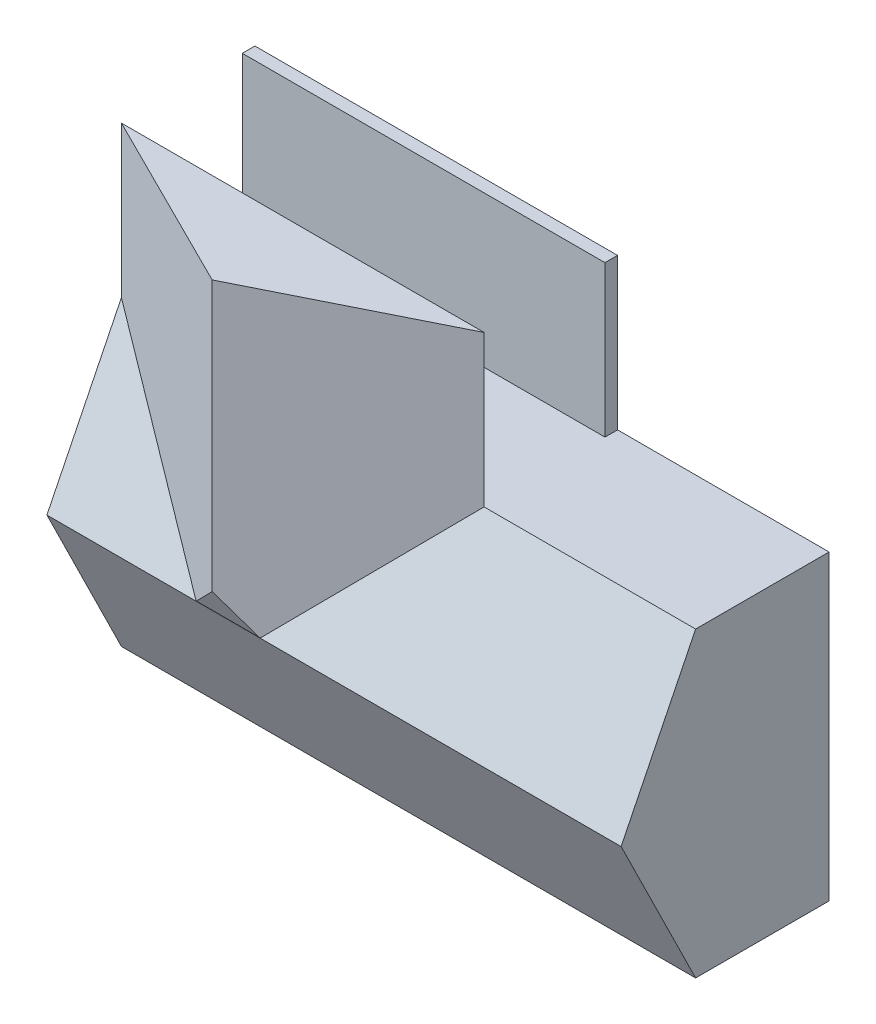
SolidWorks part; units mm, degrees
ref_plane "Front Plane" through (0, 0, 0) normal (0, 0, 1) x (1, 0, 0)
ref_plane "Top Plane" through (0, 0, 0) normal (0, 1, 0) x (1, 0, 0)
ref_plane "Right Plane" through (0, 0, 0) normal (1, 0, 0) x (0, 0, -1)
sketch "Sketch3" plane through (0, 0, 0) normal (0, 0, 1) x (1, 0, 0)
  line L0 (152.4, 152.4) -> (4550.005, 152.4)
  line L1 (0, 0) -> (11582.4, 0)
  line L2 (0, 0) -> (0, 6096)
  line L3 (0, 6096) -> (11582.4, 6096)
  line L4 (11582.4, 0) -> (11582.4, 6096)
  line L5 (4550.005, 152.4) -> (4550.005, 2596.7986)
  line L6 (4550.005, 2596.7986) -> (5842, 2596.7986)
  line L7 (11582.4, 6096) -> (7620, 6096) construction
  line L8 (7620, 6096) -> (5842, 6096) construction
  line L9 (5842, 5943.6) -> (5842, 3511.1986)
  line L10 (5943.6, 3511.1986) -> (10284.7543, 3511.1986)
  line L11 (7620, 5943.6) -> (7620, 3612.7986)
  line L12 (4550.005, 2596.7986) -> (5842, 2596.7986) construction
  line L13 (7315.2, 2495.1986) -> (7315.2, 152.4)
  line L14 (5842, 3511.1986) -> (5842, 2596.7986)
  line L15 (10386.3543, 3511.1986) -> (10386.3543, 2596.7986)
  line L16 (9786.5812, 3511.1986) -> (9786.5812, 2596.7986) construction
  line L17 (0, 6096) -> (0, 9448.8) construction
  line L18 (0, 9448.8) -> (6388.492, 9448.8) construction
  line L19 (6388.492, 9448.8) -> (6388.492, 6096) construction
  line L20 (11430, 152.4) -> (11430, 2495.1986)
  line L21 (3310.1163, 2590.8) -> (0, 2590.8) construction
  line L22 (152.4, 5943.6) -> (5842, 5943.6)
  line L23 (152.4, 152.4) -> (152.4, 5943.6)
  line L24 (4651.605, 152.4) -> (4651.605, 2495.1986)
  line L25 (4651.605, 2495.1986) -> (7315.2, 2495.1986)
  line L26 (7416.8, 2495.1986) -> (7416.8, 152.4)
  line L27 (10284.7543, 3511.1986) -> (10284.7543, 2596.7986)
  line L28 (5943.6, 3612.7986) -> (7620, 3612.7986)
  line L29 (5943.6, 5943.6) -> (5943.6, 3612.7986)
  line L30 (7721.6, 5943.6) -> (7721.6, 3612.7986)
  line L31 (7620, 6096) -> (7620, 3505.2) construction
  line L32 (7721.6, 6096) -> (7721.6, 3505.2) construction
  line L33 (5842, 6096) -> (5842, 3511.1986) construction
  line L34 (5943.6, 6096) -> (5943.6, 3511.1986) construction
  line L35 (5943.6, 5943.6) -> (7620, 5943.6)
  line L36 (152.4, 5943.6) -> (11430, 5943.6) construction
  line L37 (7721.6, 5943.6) -> (11430, 5943.6)
  line L38 (5842, 3612.7986) -> (11582.4, 3612.7986) construction
  line L39 (7721.6, 3612.7986) -> (11430, 3612.7986)
  line L40 (11430, 3612.7986) -> (11430, 5943.6)
  line L41 (11430, 152.4) -> (11430, 5943.6) construction
  line L42 (5842, 3511.1986) -> (11582.4, 3511.1986) construction
  line L43 (10386.3543, 3511.1986) -> (11430, 3511.1986)
  line L44 (10386.3543, 2596.7986) -> (11430, 2596.7986)
  line L45 (4550.005, 2596.7986) -> (11582.4, 2596.7986) construction
  line L46 (11430, 2596.7986) -> (11430, 3511.1986)
  line L47 (4651.605, 2495.1986) -> (11582.4, 2495.1986) construction
  line L48 (7315.2, 2596.7986) -> (7315.2, 0) construction
  line L49 (7416.8, 2596.7986) -> (7416.8, 0) construction
  line L50 (7416.8, 2495.1986) -> (11430, 2495.1986)
  line L51 (7416.8, 152.4) -> (11430, 152.4)
  line L52 (152.4, 152.4) -> (11430, 152.4) construction
  line L53 (4550.005, 0) -> (4550.005, 2596.7986) construction
  line L54 (4651.605, 0) -> (4651.605, 2495.1986) construction
  line L55 (4651.605, 152.4) -> (7315.2, 152.4)
  line L56 (5943.6, 3511.1986) -> (5943.6, 2596.7986)
  line L57 (5943.6, 2596.7986) -> (10284.7543, 2596.7986)
  line L58 (5943.6, 2596.7986) -> (7315.2, 2596.7986) construction
  dimension "D1" = 11582.4
  dimension "D2" = 6096
  dimension "D4" = 3962.4
  dimension "D5" = 1778
  dimension "D7" = 914.4
  dimension "D8" = 152.4
  dimension "D9" = 101.6
  dimension "D10" = 101.6
  dimension "D11" = 101.6
  dimension "D12" = 101.6
  dimension "D13" = 101.6
extrude "Boss-Extrude1" add sketch "Sketch3" along normal blind 2438.4 contours L1 L4 L3 L2 L55 L24 L25 L13 L51 L26 L50 L20 L46 L44 L15 L43 L40 L39 L30 L37 L10 L27 L6 L5 L0 L23 L22 L9 L29 L35 L11 L28
sketch "Sketch4" plane through (0, 0, 0) normal (0, 0, -1) x (-1, 0, 0)
  line L1 (-11582.4, 6096) -> (0, 6096)
  line L2 (-11582.4, 6096) -> (-11582.4, 0)
  line L3 (-11582.4, 0) -> (0, 0)
  line L4 (0, 6096) -> (0, 0)
extrude "Boss-Extrude2" add sketch "Sketch4" along normal blind 254
sketch "Sketch5" plane through (0, 0, 0) normal (0, 0, 1) x (1, 0, 0)
  line L1 (3330.805, 2596.7986) -> (152.4, 2596.7986)
  line L2 (152.4, 152.4) -> (152.4, 5943.6) construction
  line L3 (152.4, 2596.7986) -> (152.4, 2495.1986)
  line L4 (152.4, 152.4) -> (152.4, 5943.6) construction
  line L5 (152.4, 2495.1986) -> (3330.805, 2495.1986)
  line L6 (3330.805, 2495.1986) -> (3330.805, 2596.7986)
extrude "Boss-Extrude3" add sketch "Sketch5" along normal blind 1016
sketch "Sketch6" plane through (0, 0, 0) normal (-1, 0, 0) x (0, 0, 1)
  line L0 (2438.4, 6096) -> (2438.4, 0)
  line L1 (2438.4, 6096) -> (3941.5073, 3048)
  line L2 (2438.4, 3048) -> (3941.5073, 3048) construction
  line L3 (3941.5073, 3048) -> (2438.4, 0)
  dimension "D1" = 26.25
extrude "Boss-Extrude4" add sketch "Sketch6" against normal up to surface (11582.4 mm away) up to face at (11582.4, 3048, 1092.2)
sketch "Sketch7" plane through (0, 6096, 0) normal (0, 1, 0) x (1, 0, 0)
  line L0 (0, 254) -> (7315.2, 254) construction
  line L1 (0, 254) -> (11582.4, 254) construction
  line L2 (7315.2, 254) -> (7315.2, -2438.4) construction
  line L3 (0, -2438.4) -> (11582.4, -2438.4) construction
  line L4 (7937.8596, -2438.4) -> (5791.2, -3941.5073)
  line L5 (11582.4, -3941.5073) -> (0, -3941.5073) construction
  line L6 (5791.2, -3941.5073) -> (5791.2, -2438.4) construction
  line L7 (3644.5404, -2438.4) -> (5791.2, -3941.5073)
  line L8 (7937.8596, -2438.4) -> (3644.5404, -2438.4)
  dimension "D1" = 55
sketch "Sketch8" plane through (0, 0, -254) normal (0, 0, -1) x (-1, 0, 0)
  line L1 (0, 6096) -> (-7315.2, 6096)
  line L2 (0, 6096) -> (0, 9144)
  line L3 (0, 9144) -> (-7315.2, 9144)
  line L4 (-7315.2, 6096) -> (-7315.2, 9144)
  dimension "D1" = 7315.2
  dimension "D2" = 3048
extrude "Boss-Extrude6" add sketch "Sketch8" against normal blind 254 separate body
sketch "Sketch9" plane through (0, 0, 0) normal (-1, 0, 0) x (0, 0, 1)
  line L0 (2438.4, 0) -> (4693.0609, 4572)
  line L1 (2438.4, 0) -> (2438.4, 9144)
  line L2 (2438.4, 4572) -> (4693.0609, 4572) construction
  line L3 (2438.4, 9144) -> (4693.0609, 4572)
sketch "Sketch10" plane through (0, 9144, 0) normal (0, 1, 0) x (1, 0, 0)
  line L0 (7315.2, -2438.4) -> (0, -2438.4)
  line L1 (3644.5404, -2438.4) -> (3657.6, -4693.0609) construction
  line L2 (7315.2, -4693.0609) -> (0, -4693.0609) construction
  line L5 (7315.2, -2438.4) -> (3655.1104, -4263.2533)
  line L6 (3655.1104, -4263.2533) -> (0, -2438.4)
  dimension "D1" = 26.5
extrude "Boss-Extrude7" add sketch "Sketch10" against normal blind 6085.84
sketch "Sketch11" plane through (0, -967.2564, 1961.4019) normal (0, -0.4423, 0.8969) x (1, 0, 0)
  line L1 (5444.9184, 4256.1108) -> (2083.927, 4256.1108)
  line L2 (5444.9184, 4256.1108) -> (5444.9184, 5301.5124)
  line L3 (5444.9184, 5301.5124) -> (2083.927, 5301.5124)
  line L4 (2083.927, 4256.1108) -> (2083.927, 5301.5124)
extrude "Cut-Extrude1" cut sketch "Sketch11" along normal blind 6085.84
